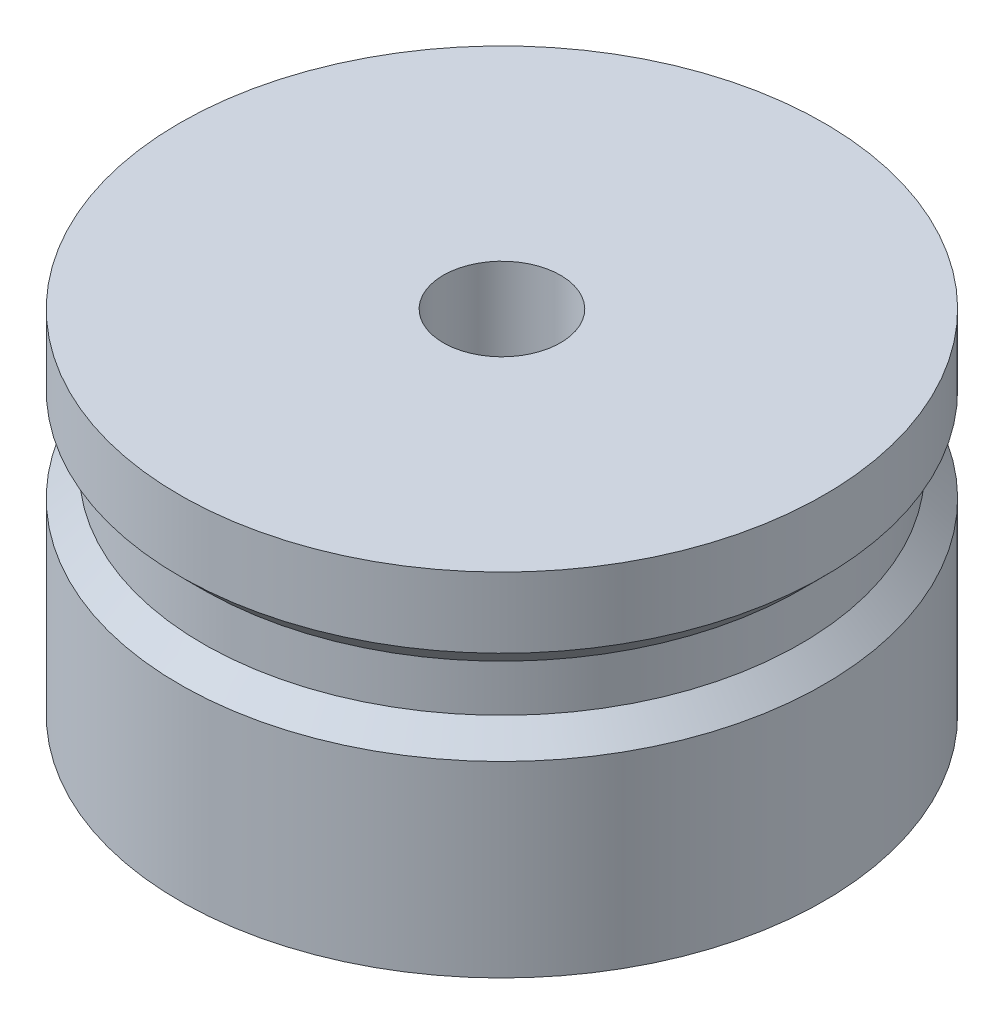
SolidWorks part; units mm, degrees
material "Liga de aço"
ref_plane "Plano frontal" through (0, 0, 0) normal (0, 0, 1) x (1, 0, 0)
ref_plane "Plano superior" through (0, 0, 0) normal (0, 1, 0) x (1, 0, 0)
ref_plane "Plano direito" through (0, 0, 0) normal (1, 0, 0) x (0, 0, -1)
sketch "Esboço1" plane through (0, 0, 0) normal (0, 0, 1) x (1, 0, 0)
  line L0 (0, 0) -> (0, -30) construction
  line L1 (5, 0) -> (5, -30)
  line L2 (5, -30) -> (27.5, -30)
  line L3 (27.5, -30) -> (27.5, -14)
  line L4 (27.5, -14) -> (25.5, -12)
  line L5 (25.5, -12) -> (25.5, -8)
  line L6 (25.5, -8) -> (27.5, -6)
  line L7 (27.5, -6) -> (27.5, 0)
  line L8 (27.5, 0) -> (5, 0)
  dimension "D1" = 30
  dimension "D2" = 10
  dimension "D3" = 55
  dimension "D4" = 6
  dimension "D5" = 8
  dimension "D6" = 2
revolve "Revolução1" add sketch "Esboço1" angle 360 about L0
